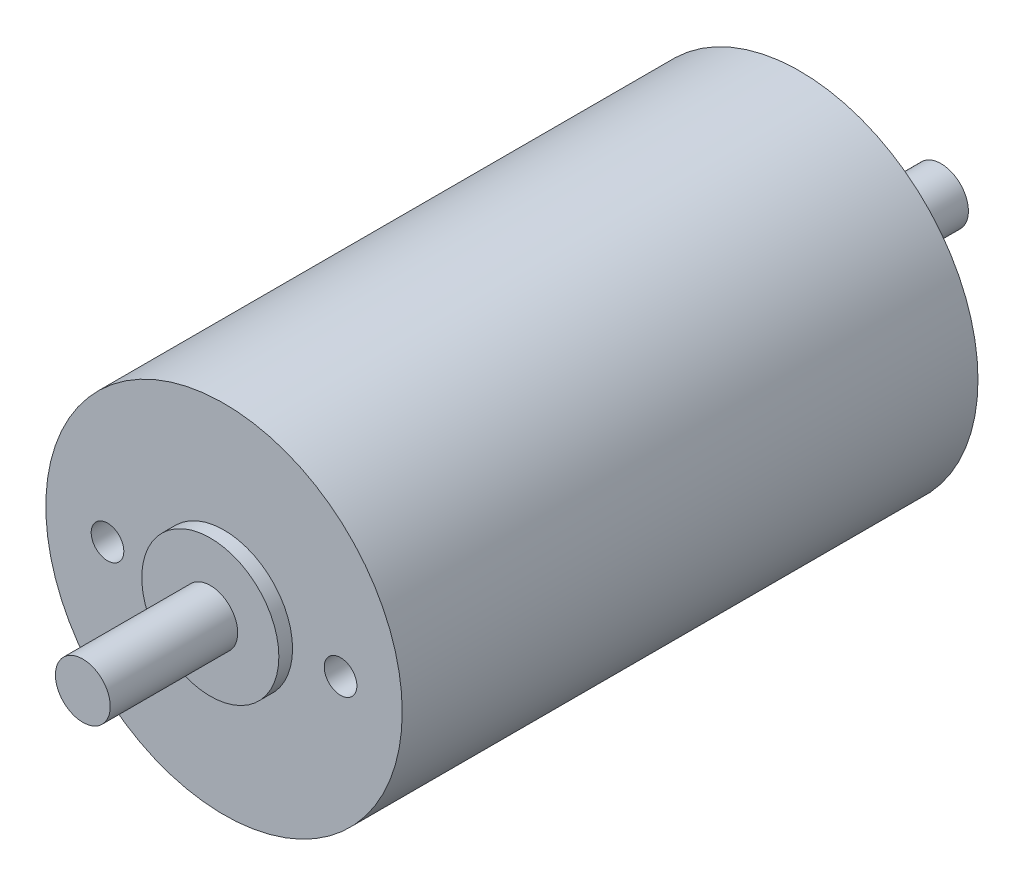
SolidWorks part; units mm, degrees
ref_plane "Front Plane" through (0, 0, 0) normal (1, 0, 0) x (0, 1, 0)
ref_plane "Top Plane" through (0, 0, 0) normal (0, 0, 1) x (0, 1, 0)
ref_plane "Right Plane" through (0, 0, 0) normal (0, 1, 0) x (-1, 0, 0)
sketch "Sketch1" plane through (0, 0, 0) normal (0, 0, 1) x (0, 1, 0)
  circle A0 centre (0, 0) radius 13
  dimension "D1" = 26
extrude "Boss-Extrude1" add sketch "Sketch1" along normal mid plane 42
sketch "Sketch2" plane through (0, 0, 21) normal (0, 0, 1) x (1, 0, 0)
  circle A0 centre (0, 0) radius 5
  dimension "D1" = 10
extrude "Boss-Extrude2" add sketch "Sketch2" along normal blind 1
sketch "Sketch3" plane through (0, 0, 22) normal (0, 0, 1) x (1, 0, 0)
  circle A0 centre (0, 0) radius 2
  dimension "D1" = 4
sketch "Sketch4" plane through (0, 0, -21) normal (0, 0, -1) x (1, 0, 0)
  circle A0 centre (0, 0) radius 5.5
  dimension "D1" = 11
extrude "Boss-Extrude4" add sketch "Sketch4" along normal blind 1
extrude "Boss-Extrude5" add sketch "Sketch3" along normal blind 9.3
sketch "Sketch5" plane through (0, 0, -22) normal (0, 0, -1) x (1, 0, 0)
  circle A0 centre (0, 0) radius 2
  dimension "D1" = 4
extrude "Boss-Extrude6" add sketch "Sketch5" along normal blind 9.3
hole_wizard "3/32 (0.09375) Diameter Hole1" positions "Sketch7" profile "Sketch8" hole size "3/32" standard "ANSI Inch"
sketch "Sketch7" plane through (0, 0, 21) normal (0, 0, 1) x (1, 0, 0)
  line L0 (0, 0) -> (-8.5, 0) construction
  line L2 (0, 0) -> (8.5, 0) construction
  point P0 (8.5, 0)
  point P2 (-8.5, 0)
  dimension "D1" = 17
sketch "Sketch8" plane through (8.5, 0, 21) normal (1, 0, 0) x (0, -1, 0)
  line L0 (0, 0) -> (0, 13.4154)
  line L1 (0, 13.4154) -> (1.1906, 12.7)
  line L2 (1.1906, 12.7) -> (1.1906, 0)
  line L5 (1.1906, 0) -> (0, 0)
  line L10 (0, 13.4154) -> (-1.1906, 12.7) construction
  line L11 (0, -6.35) -> (0, 107.95) construction
  dimension "Hole Dia." = 2.3812
  dimension "Hole Depth" = 12.7
  dimension "Drill Angle" = 118
